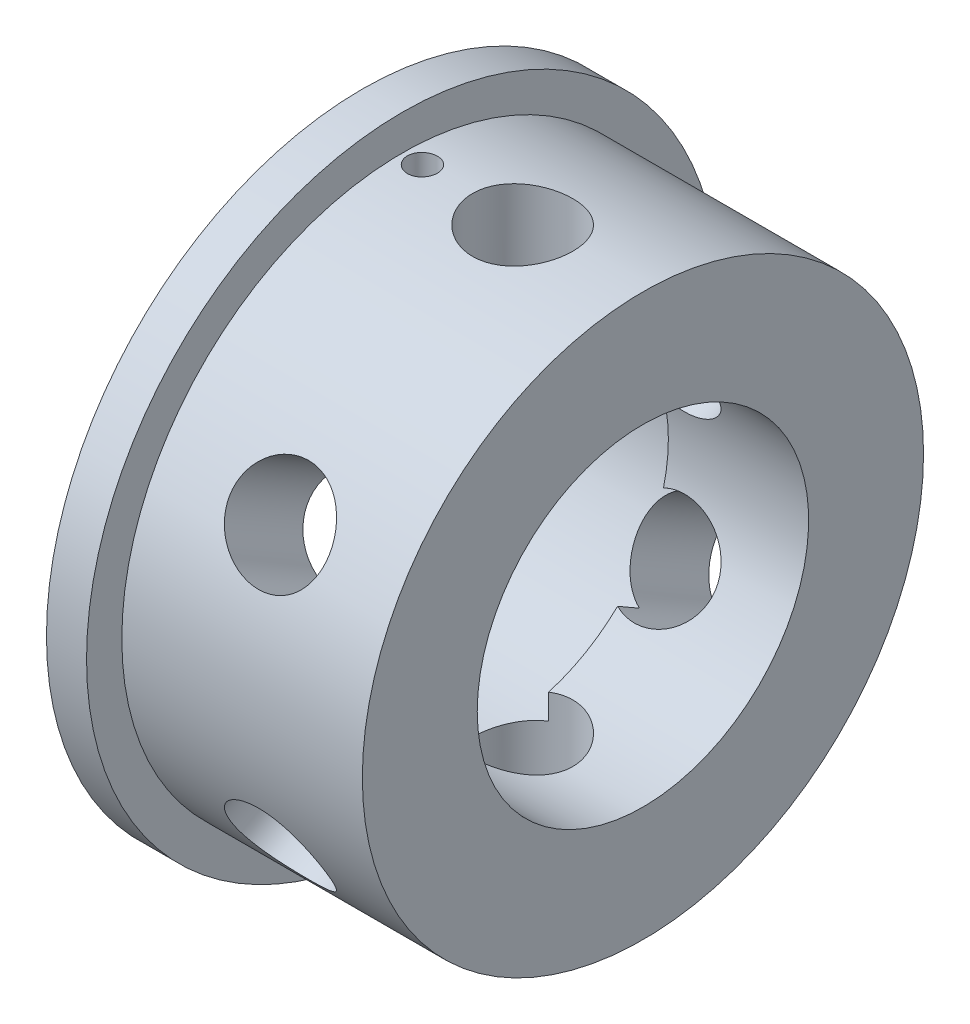
SolidWorks part; units mm, degrees
ref_plane "Front Plane" through (0, 0, 0) normal (0, 0, 1) x (1, 0, 0)
ref_plane "Top Plane" through (0, 0, 0) normal (0, 1, 0) x (1, 0, 0)
ref_plane "Right Plane" through (0, 0, 0) normal (1, 0, 0) x (0, 0, -1)
sketch "Sketch0" plane through (0, 0, 0) normal (0, 0, 1) x (1, 0, 0)
  line L0 (-44.45, 0) -> (0, 0) construction
  line L2 (-38.1, 44.45) -> (-38.1, -44.45) construction
  line L3 (-38.1, 50.038) -> (-38.1, -50.038) construction
  line L4 (-44.45, 34.3535) -> (-44.45, -34.3535) construction
  line L5 (-22.225, 30.099) -> (-44.45, 30.2895) construction
  line L6 (-22.225, 30.099) -> (-22.225, -30.099) construction
  line L7 (-22.225, -30.099) -> (-44.45, -30.2895) construction
  line L8 (-44.45, 30.2895) -> (-44.45, -30.2895) construction
  line L14 (-22.225, 26.2509) -> (-22.225, -26.2509) construction
  line L15 (-22.225, -26.2509) -> (-22.225, -30.3149) construction
  line L16 (-44.45, -30.2895) -> (-44.45, -34.3535) construction
  line L21 (-44.45, 0) -> (-22.225, 0) construction
  point P12 (-38.1, 0)
  dimension "A" = 44.45
  dimension "OD A 2" = 60.579
  dimension "OD B 2" = 60.198
  dimension "ID 2" = 52.5018
  dimension "H 2" = 4.064
  dimension "B" = 22.225
  dimension "Pipe OD 1" = 88.9
  dimension "C 1" = 38.1
  dimension "H 1" = 5.588
sketch "Sketch1" plane through (0, 0, 0) normal (0, 0, 1) x (1, 0, 0)
  line L0 (-44.45, 0) -> (0, 0) construction
  line L1 (-44.45, 0) -> (0, 0) construction
  line L2 (-38.1, -44.45) -> (0, -44.45)
  line L3 (0, -26.2509) -> (0, -44.45)
  line L4 (-44.45, -34.3535) -> (-44.45, -30.2895)
  line L5 (-44.45, -30.2895) -> (-22.225, -30.099)
  line L6 (0, 0) -> (0, -26.2509) construction
  line L7 (-44.45, -34.3535) -> (-44.45, -50.038)
  line L8 (-22.225, -26.2509) -> (-22.225, -30.099)
  line L9 (-44.45, -50.038) -> (-38.1, -50.038)
  line L10 (-38.1, -50.038) -> (-38.1, -44.45)
  line L11 (-22.225, -26.2509) -> (0, -26.2509)
  line L12 (-38.1, 44.45) -> (-38.1, -44.45) construction
revolve "Revolve1" add sketch "Sketch1" angle 360 about L1
hole_wizard "5/8 (0.625) Diameter Hole1" positions "Sketch3" profile "Sketch2" hole size "5/8" standard "ANSI Inch"
sketch "Sketch3" plane through (0, 0, 0) normal (0, 1, 0) x (1, 0, 0)
  point P0 (-19.05, 0)
  dimension "D1" = 19.05
sketch "Sketch2" plane through (-19.05, 0, 0) normal (1, 0, 0) x (0, 0, -1)
  line L0 (0, 0) -> (0, 68.3532)
  line L1 (0, 68.3532) -> (7.9375, 68.3532)
  line L2 (7.9375, 68.3532) -> (7.9375, 0)
  line L5 (7.9375, 0) -> (0, 0)
  line L11 (0, -6.35) -> (0, 107.95) construction
  dimension "Thru Hole Dia." = 15.875
  dimension "Thru Hole Depth" = 68.3532
ref_axis "Axis1" through (-44.45, 0, 0) along (1, 0, 0)
pattern_circular "CirPattern1" count 6 over 360 about axis through (-44.45, 0, 0) along (1, 0, 0) of "5/8 (0.625) Diameter Hole1"
sketch "Sketch4" plane through (0, 0, 0) normal (0, 1, 0) x (1, 0, 0)
  circle A0 centre (-34.925, 0) radius 2.3812
  dimension "D1" = 4.7625
  dimension "D2" = 34.925
extrude "Cut-Extrude1" cut sketch "Sketch4" against normal through all both and the other way through all
